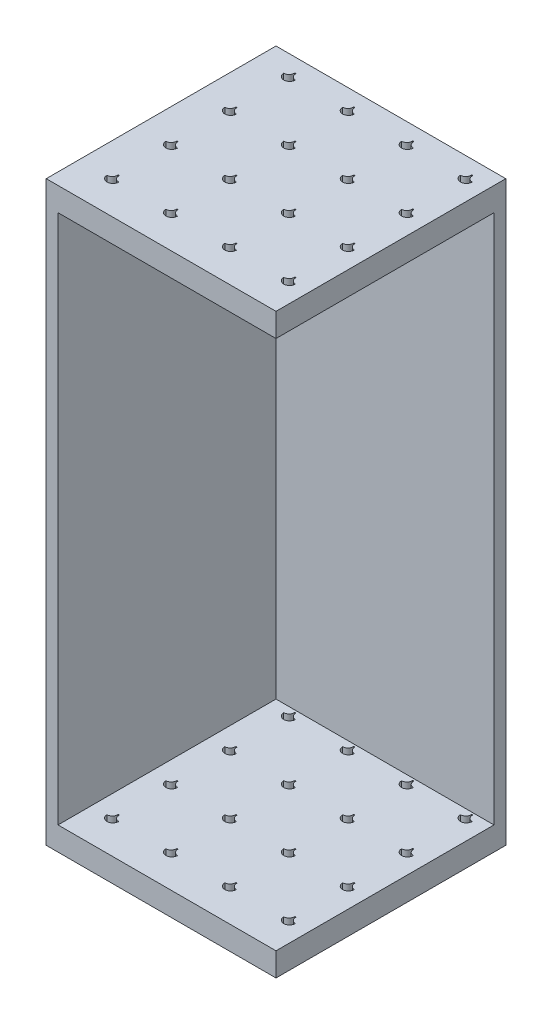
SolidWorks part; units mm, degrees
ref_plane "Front Plane" through (0, 0, 0) normal (0, 0, 1) x (1, 0, 0)
ref_plane "Top Plane" through (0, 0, 0) normal (0, 1, 0) x (1, 0, 0)
ref_plane "Right Plane" through (0, 0, 0) normal (1, 0, 0) x (0, 0, -1)
sketch "Sketch1" plane through (0, 0, 0) normal (0, 1, 0) x (1, 0, 0)
  line L1 (9.75, -9.75) -> (-9.75, -9.75)
  line L2 (9.75, -9.75) -> (9.75, 9.75)
  line L3 (9.75, 9.75) -> (-9.75, 9.75)
  line L4 (-9.75, -9.75) -> (-9.75, 9.75)
  line L5 (9.75, -9.75) -> (-9.75, 9.75) construction
  line L6 (9.75, 9.75) -> (-9.75, -9.75) construction
  point P0 (0, 0)
  dimension "D2" = 19.5
extrude "Boss-Extrude1" add sketch "Sketch1" along normal blind 2
sketch "Sketch2" plane through (0, 2, 0) normal (0, 1, 0) x (1, 0, 0)
  line L0 (-9.75, 9.75) -> (9.75, -9.75) construction
  line L1 (9.75, 9.75) -> (-9.75, -9.75) construction
  line L6 (9.75, -9.75) -> (9.75, 9.75) construction
  line L7 (9.75, 8.75) -> (-8.75, 8.75)
  line L8 (-8.75, 8.75) -> (-8.75, -9.75)
  line L9 (-9.75, -9.75) -> (9.75, -9.75) construction
  line L10 (-8.75, -9.75) -> (-9.75, -9.75)
  line L11 (-9.75, -9.75) -> (-9.75, 9.75)
  line L12 (-9.75, 9.75) -> (9.75, 9.75)
  line L13 (9.75, 9.75) -> (9.75, 8.75)
  dimension "D1" = 1
extrude "Boss-Extrude2" add sketch "Sketch2" along normal blind 45
sketch "Sketch3" plane through (0, 0, 0) normal (0, -1, 0) x (1, 0, 0)
  line L0 (-9.75, 9.75) -> (9.75, -9.75) construction
  line L1 (9.75, 9.75) -> (-9.75, -9.75) construction
  line L2 (-7.4216, 6.9216) -> (-6.4216, 6.9216) construction
  line L3 (-6.9216, 6.4216) -> (-6.9216, 7.4216) construction
  line L4 (-6.9216, 6.4716) -> (-6.9716, 6.4716) construction
  line L5 (-6.9716, 6.4716) -> (-6.9716, 6.4241)
  line L6 (-6.8716, 6.4716) -> (-6.8716, 6.4241)
  line L7 (-1.8716, 6.4716) -> (-1.8716, 6.4241)
  line L8 (-1.9716, 6.4716) -> (-1.9716, 6.4241)
  line L9 (3.1284, 6.4716) -> (3.1284, 6.4241)
  line L10 (3.0284, 6.4716) -> (3.0284, 6.4241)
  line L11 (8.1284, 6.4716) -> (8.1284, 6.4241)
  line L12 (8.0284, 6.4716) -> (8.0284, 6.4241)
  line L13 (-1.8716, 1.4716) -> (-1.8716, 1.4241)
  line L14 (-1.9716, 1.4716) -> (-1.9716, 1.4241)
  line L15 (3.1284, 1.4716) -> (3.1284, 1.4241)
  line L16 (3.0284, 1.4716) -> (3.0284, 1.4241)
  line L17 (8.1284, 1.4716) -> (8.1284, 1.4241)
  line L18 (8.0284, 1.4716) -> (8.0284, 1.4241)
  line L19 (-1.8716, -3.5284) -> (-1.8716, -3.5759)
  line L20 (-1.9716, -3.5284) -> (-1.9716, -3.5759)
  line L21 (3.1284, -3.5284) -> (3.1284, -3.5759)
  line L22 (3.0284, -3.5284) -> (3.0284, -3.5759)
  line L23 (8.1284, -3.5284) -> (8.1284, -3.5759)
  line L24 (8.0284, -3.5284) -> (8.0284, -3.5759)
  line L25 (-1.8716, -8.5284) -> (-1.8716, -8.5759)
  line L26 (-1.9716, -8.5284) -> (-1.9716, -8.5759)
  line L27 (3.1284, -8.5284) -> (3.1284, -8.5759)
  line L28 (3.0284, -8.5284) -> (3.0284, -8.5759)
  line L29 (8.1284, -8.5284) -> (8.1284, -8.5759)
  line L30 (8.0284, -8.5284) -> (8.0284, -8.5759)
  line L31 (-6.8716, 1.4716) -> (-6.8716, 1.4241)
  line L32 (-6.9716, 1.4716) -> (-6.9716, 1.4241)
  line L33 (-6.8716, -3.5284) -> (-6.8716, -3.5759)
  line L34 (-6.9716, -3.5284) -> (-6.9716, -3.5759)
  line L35 (-6.8716, -8.5284) -> (-6.8716, -8.5759)
  line L36 (-6.9716, -8.5284) -> (-6.9716, -8.5759)
  arc A0 (-6.9716, 6.4241) -> (-6.8716, 6.4241) centre (-6.9216, 6.9216) ccw
  arc A1 (-7.4216, 6.9216) -> (-6.9716, 6.4716) centre (-7.4216, 6.4716) cw
  arc A2 (-6.4216, 6.9216) -> (-6.8716, 6.4716) centre (-6.4216, 6.4716) ccw
  arc A3 (-6.4216, 6.9216) -> (-7.4216, 6.9216) centre (-6.9216, 6.9216) ccw
  arc A4 (-1.4216, 6.9216) -> (-2.4216, 6.9216) centre (-1.9216, 6.9216) ccw
  arc A5 (-2.4216, 6.9216) -> (-1.9716, 6.4716) centre (-2.4216, 6.4716) cw
  arc A6 (-1.4216, 6.9216) -> (-1.8716, 6.4716) centre (-1.4216, 6.4716) ccw
  arc A7 (-1.9716, 6.4241) -> (-1.8716, 6.4241) centre (-1.9216, 6.9216) ccw
  arc A8 (3.5784, 6.9216) -> (2.5784, 6.9216) centre (3.0784, 6.9216) ccw
  arc A9 (2.5784, 6.9216) -> (3.0284, 6.4716) centre (2.5784, 6.4716) cw
  arc A10 (3.5784, 6.9216) -> (3.1284, 6.4716) centre (3.5784, 6.4716) ccw
  arc A11 (3.0284, 6.4241) -> (3.1284, 6.4241) centre (3.0784, 6.9216) ccw
  arc A12 (8.5784, 6.9216) -> (7.5784, 6.9216) centre (8.0784, 6.9216) ccw
  arc A13 (7.5784, 6.9216) -> (8.0284, 6.4716) centre (7.5784, 6.4716) cw
  arc A14 (8.5784, 6.9216) -> (8.1284, 6.4716) centre (8.5784, 6.4716) ccw
  arc A15 (8.0284, 6.4241) -> (8.1284, 6.4241) centre (8.0784, 6.9216) ccw
  arc A16 (-1.4216, 1.9216) -> (-2.4216, 1.9216) centre (-1.9216, 1.9216) ccw
  arc A17 (-2.4216, 1.9216) -> (-1.9716, 1.4716) centre (-2.4216, 1.4716) cw
  arc A18 (-1.4216, 1.9216) -> (-1.8716, 1.4716) centre (-1.4216, 1.4716) ccw
  arc A19 (-1.9716, 1.4241) -> (-1.8716, 1.4241) centre (-1.9216, 1.9216) ccw
  arc A20 (3.5784, 1.9216) -> (2.5784, 1.9216) centre (3.0784, 1.9216) ccw
  arc A21 (2.5784, 1.9216) -> (3.0284, 1.4716) centre (2.5784, 1.4716) cw
  arc A22 (3.5784, 1.9216) -> (3.1284, 1.4716) centre (3.5784, 1.4716) ccw
  arc A23 (3.0284, 1.4241) -> (3.1284, 1.4241) centre (3.0784, 1.9216) ccw
  arc A24 (8.5784, 1.9216) -> (7.5784, 1.9216) centre (8.0784, 1.9216) ccw
  arc A25 (7.5784, 1.9216) -> (8.0284, 1.4716) centre (7.5784, 1.4716) cw
  arc A26 (8.5784, 1.9216) -> (8.1284, 1.4716) centre (8.5784, 1.4716) ccw
  arc A27 (8.0284, 1.4241) -> (8.1284, 1.4241) centre (8.0784, 1.9216) ccw
  arc A28 (-1.4216, -3.0784) -> (-2.4216, -3.0784) centre (-1.9216, -3.0784) ccw
  arc A29 (-2.4216, -3.0784) -> (-1.9716, -3.5284) centre (-2.4216, -3.5284) cw
  arc A30 (-1.4216, -3.0784) -> (-1.8716, -3.5284) centre (-1.4216, -3.5284) ccw
  arc A31 (-1.9716, -3.5759) -> (-1.8716, -3.5759) centre (-1.9216, -3.0784) ccw
  arc A32 (3.5784, -3.0784) -> (2.5784, -3.0784) centre (3.0784, -3.0784) ccw
  arc A33 (2.5784, -3.0784) -> (3.0284, -3.5284) centre (2.5784, -3.5284) cw
  arc A34 (3.5784, -3.0784) -> (3.1284, -3.5284) centre (3.5784, -3.5284) ccw
  arc A35 (3.0284, -3.5759) -> (3.1284, -3.5759) centre (3.0784, -3.0784) ccw
  arc A36 (8.5784, -3.0784) -> (7.5784, -3.0784) centre (8.0784, -3.0784) ccw
  arc A37 (7.5784, -3.0784) -> (8.0284, -3.5284) centre (7.5784, -3.5284) cw
  arc A38 (8.5784, -3.0784) -> (8.1284, -3.5284) centre (8.5784, -3.5284) ccw
  arc A39 (8.0284, -3.5759) -> (8.1284, -3.5759) centre (8.0784, -3.0784) ccw
  arc A40 (-1.4216, -8.0784) -> (-2.4216, -8.0784) centre (-1.9216, -8.0784) ccw
  arc A41 (-2.4216, -8.0784) -> (-1.9716, -8.5284) centre (-2.4216, -8.5284) cw
  arc A42 (-1.4216, -8.0784) -> (-1.8716, -8.5284) centre (-1.4216, -8.5284) ccw
  arc A43 (-1.9716, -8.5759) -> (-1.8716, -8.5759) centre (-1.9216, -8.0784) ccw
  arc A44 (3.5784, -8.0784) -> (2.5784, -8.0784) centre (3.0784, -8.0784) ccw
  arc A45 (2.5784, -8.0784) -> (3.0284, -8.5284) centre (2.5784, -8.5284) cw
  arc A46 (3.5784, -8.0784) -> (3.1284, -8.5284) centre (3.5784, -8.5284) ccw
  arc A47 (3.0284, -8.5759) -> (3.1284, -8.5759) centre (3.0784, -8.0784) ccw
  arc A48 (8.5784, -8.0784) -> (7.5784, -8.0784) centre (8.0784, -8.0784) ccw
  arc A49 (7.5784, -8.0784) -> (8.0284, -8.5284) centre (7.5784, -8.5284) cw
  arc A50 (8.5784, -8.0784) -> (8.1284, -8.5284) centre (8.5784, -8.5284) ccw
  arc A51 (8.0284, -8.5759) -> (8.1284, -8.5759) centre (8.0784, -8.0784) ccw
  arc A52 (-6.4216, 1.9216) -> (-7.4216, 1.9216) centre (-6.9216, 1.9216) ccw
  arc A53 (-7.4216, 1.9216) -> (-6.9716, 1.4716) centre (-7.4216, 1.4716) cw
  arc A54 (-6.4216, 1.9216) -> (-6.8716, 1.4716) centre (-6.4216, 1.4716) ccw
  arc A55 (-6.9716, 1.4241) -> (-6.8716, 1.4241) centre (-6.9216, 1.9216) ccw
  arc A56 (-6.4216, -3.0784) -> (-7.4216, -3.0784) centre (-6.9216, -3.0784) ccw
  arc A57 (-7.4216, -3.0784) -> (-6.9716, -3.5284) centre (-7.4216, -3.5284) cw
  arc A58 (-6.4216, -3.0784) -> (-6.8716, -3.5284) centre (-6.4216, -3.5284) ccw
  arc A59 (-6.9716, -3.5759) -> (-6.8716, -3.5759) centre (-6.9216, -3.0784) ccw
  arc A60 (-6.4216, -8.0784) -> (-7.4216, -8.0784) centre (-6.9216, -8.0784) ccw
  arc A61 (-7.4216, -8.0784) -> (-6.9716, -8.5284) centre (-7.4216, -8.5284) cw
  arc A62 (-6.4216, -8.0784) -> (-6.8716, -8.5284) centre (-6.4216, -8.5284) ccw
  arc A63 (-6.9716, -8.5759) -> (-6.8716, -8.5759) centre (-6.9216, -8.0784) ccw
  dimension "D1" = 1
  dimension "D2" = 0.05
  dimension "D3" = 0.05
  dimension "D4" = 4
  dimension "D5" = 4
  dimension "D6" = 4
sketch "Sketch5" plane through (0, 47, 0) normal (0, 1, 0) x (1, 0, 0)
  line L1 (9.75, -9.75) -> (-9.75, -9.75)
  line L2 (9.75, -9.75) -> (9.75, 9.75)
  line L3 (9.75, 9.75) -> (-9.75, 9.75)
  line L4 (-9.75, -9.75) -> (-9.75, 9.75)
  line L5 (9.75, -9.75) -> (-9.75, 9.75) construction
  line L6 (9.75, 9.75) -> (-9.75, -9.75) construction
  point P0 (0, 0)
extrude "Boss-Extrude5" add sketch "Sketch5" along normal blind 2
extrude "Cut-Extrude1" cut sketch "Sketch3" against normal through all
